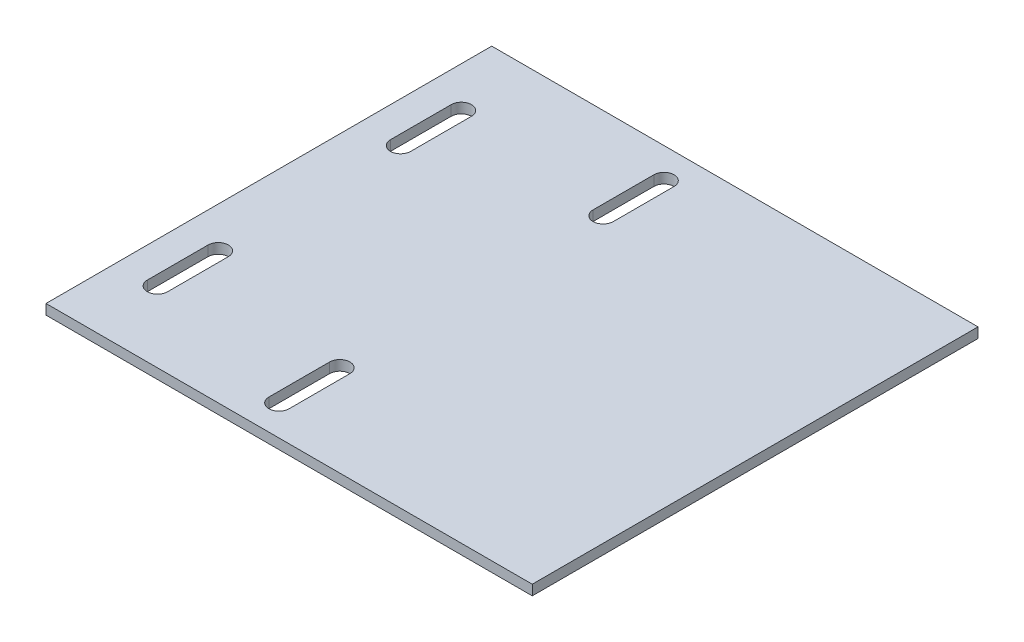
SolidWorks part; units mm, degrees
material "ASTM A36 Steel"
ref_plane "Front Plane" through (0, 0, 0) normal (0, 0, 1) x (1, 0, 0)
ref_plane "Top Plane" through (0, 0, 0) normal (0, 1, 0) x (1, 0, 0)
ref_plane "Right Plane" through (0, 0, 0) normal (1, 0, 0) x (0, 0, -1)
sketch "Sketch1" plane through (0, 0, 0) normal (0, 1, 0) x (1, 0, 0)
  line L1 (76.2, 69.85) -> (-76.2, 69.85)
  line L2 (76.2, 69.85) -> (76.2, -69.85)
  line L3 (76.2, -69.85) -> (-76.2, -69.85)
  line L4 (-76.2, 69.85) -> (-76.2, -69.85)
  line L5 (76.2, 69.85) -> (-76.2, -69.85) construction
  line L6 (76.2, -69.85) -> (-76.2, 69.85) construction
  point P0 (0, 0)
  dimension "D1" = 139.7
  dimension "D2" = 152.4
extrude "Boss-Extrude1" add sketch "Sketch1" along normal blind 3.175
sketch "Sketch2" plane through (0, 3.175, 0) normal (0, 1, 0) x (1, 0, 0)
  line L0 (-76.2, 69.85) -> (-76.2, -69.85) construction
  line L1 (-2.6194, 0) -> (2.6194, 0) construction
  line L6 (-63.5, -38.1) -> (-63.5, 38.1) construction
  line L8 (-12.7, -50.8) -> (-12.7, 50.8) construction
  line L9 (-63.5, -38.1) -> (-12.7, 50.8) construction
  line L10 (-63.5, 38.1) -> (-12.7, -50.8) construction
  line L12 (-12.7, -41.275) -> (-12.7, -60.325) construction
  line L13 (-9.525, -41.275) -> (-9.525, -60.325)
  line L14 (-15.875, -41.275) -> (-15.875, -60.325)
  line L15 (-12.7, 41.275) -> (-12.7, 60.325) construction
  line L16 (-15.875, 41.275) -> (-15.875, 60.325)
  line L17 (-9.525, 41.275) -> (-9.525, 60.325)
  line L18 (-63.5, -28.575) -> (-63.5, -47.625) construction
  line L19 (-60.325, -28.575) -> (-60.325, -47.625)
  line L20 (-66.675, -28.575) -> (-66.675, -47.625)
  line L21 (-63.5, 47.625) -> (-63.5, 28.575) construction
  line L22 (-60.325, 47.625) -> (-60.325, 28.575)
  line L23 (-66.675, 47.625) -> (-66.675, 28.575)
  arc A0 (-9.525, -41.275) -> (-15.875, -41.275) centre (-12.7, -41.275) ccw
  arc A1 (-15.875, -60.325) -> (-9.525, -60.325) centre (-12.7, -60.325) ccw
  arc A2 (-15.875, 41.275) -> (-9.525, 41.275) centre (-12.7, 41.275) ccw
  arc A3 (-9.525, 60.325) -> (-15.875, 60.325) centre (-12.7, 60.325) ccw
  arc A4 (-60.325, -28.575) -> (-66.675, -28.575) centre (-63.5, -28.575) ccw
  arc A5 (-66.675, -47.625) -> (-60.325, -47.625) centre (-63.5, -47.625) ccw
  arc A6 (-60.325, 47.625) -> (-66.675, 47.625) centre (-63.5, 47.625) ccw
  arc A7 (-66.675, 28.575) -> (-60.325, 28.575) centre (-63.5, 28.575) ccw
  point P0 (-41.7286, 0)
  point P7 (-63.5, 0)
  point P11 (-12.7, -50.8)
  point P18 (-12.7, 50.8)
  point P27 (-63.5, -38.1)
  point P34 (-63.5, 38.1)
  dimension "D1" = 63.5
  dimension "D2" = 101.6
  dimension "D3" = 19.05
  dimension "D4" = 6.35
  dimension "D5" = 50.8
  dimension "D6" = 76.2
extrude "Cut-Extrude1" cut sketch "Sketch2" against normal through all contours L14 A1 L13 A0 | L17 A3 L16 A2 | L20 A5 L19 A4 | L23 A7 L22 A6
ref_plane "Plane1" through (-76.2, 3.175, -69.85) normal (-1, 0, 0) x (0, 0, 1)
sketch3d "TAG"
  line L0 (-76.2, 3.175, -69.85) -> (-76.2, 0, -69.85) construction
  line L1 (-76.2, 3.175, -69.85) -> (-76.2, 3.175, 69.85) construction
  line L2 (76.2, 3.175, -69.85) -> (-76.2, 3.175, -69.85) construction
  line L3 (-76.2, 3.175, -69.85) -> (-76.2, 0, -69.85)
  line L4 (-76.2, 3.175, -69.85) -> (-76.2, 3.175, 69.85)
  line L5 (76.2, 3.175, -69.85) -> (-76.2, 3.175, -69.85)
  dimension "D1" = 3.175
  dimension "D2" = 139.7
  dimension "D3" = 152.4
